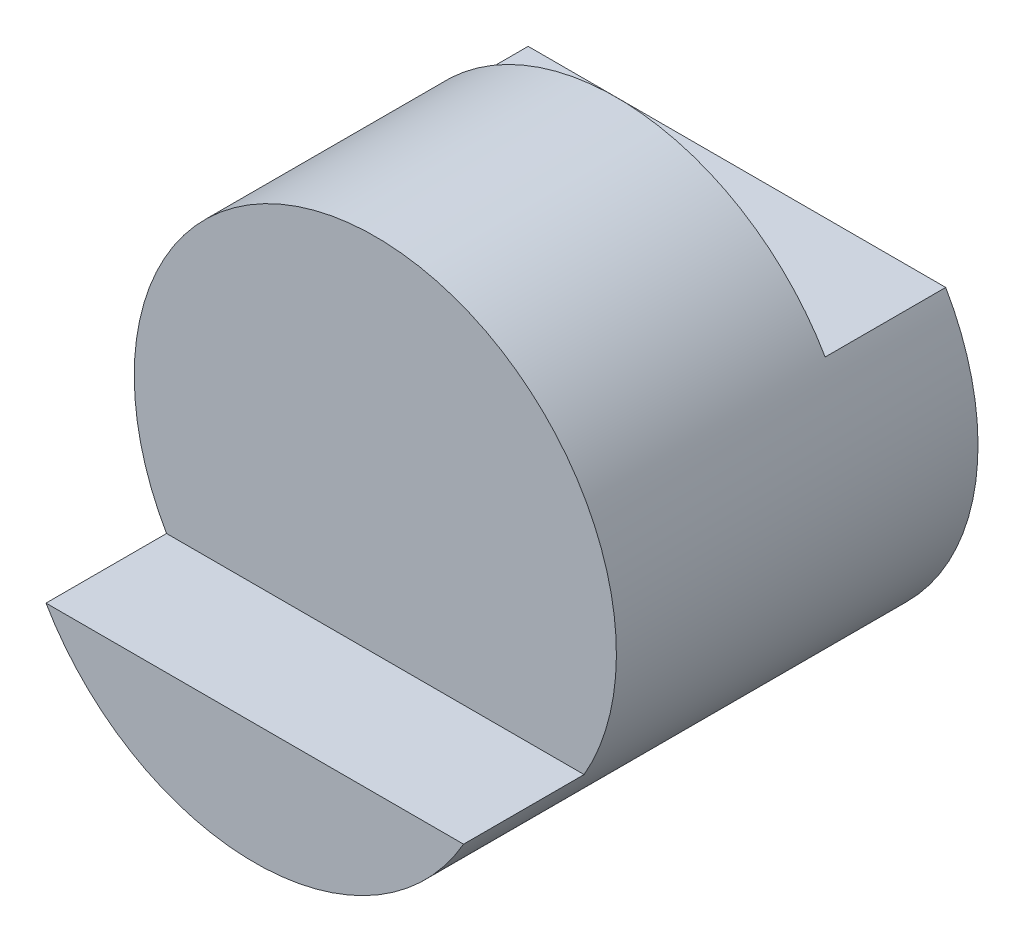
SolidWorks part; units mm, degrees
ref_plane "Front" through (0, 0, 0) normal (0, 0, 1) x (1, 0, 0)
ref_plane "Top" through (0, 0, 0) normal (0, 1, 0) x (1, 0, 0)
ref_plane "Right" through (0, 0, 0) normal (1, 0, 0) x (0, 0, -1)
sketch "Sketch1" plane through (0, 0, 0) normal (0, 0, 1) x (1, 0, 0)
  circle A0 centre (0, 0) radius 2
  dimension "D1" = 4
extrude "Boss-Extrude1" add sketch "Sketch1" along normal blind 3
sketch "Sketch2" plane through (0, 0, 3) normal (0, 0, 1) x (1, 0, 0)
  line L1 (-1.7321, -1) -> (1.7321, -1)
  circle A0 centre (0, 0) radius 2 construction
  arc A2 (-1.7321, -1) -> (1.7321, -1) centre (0, 0) ccw
  dimension "D1" = 1
extrude "Boss-Extrude2" add sketch "Sketch2" along normal blind 1
sketch "Sketch3" plane through (0, 0, 0) normal (0, 0, -1) x (-1, 0, 0)
  line L0 (1.7321, 1) -> (-1.7321, 1)
  arc A0 (1.7321, 1) -> (-1.7321, 1) centre (0, 0) ccw
extrude "Cut-Extrude1" cut sketch "Sketch3" against normal blind 1
